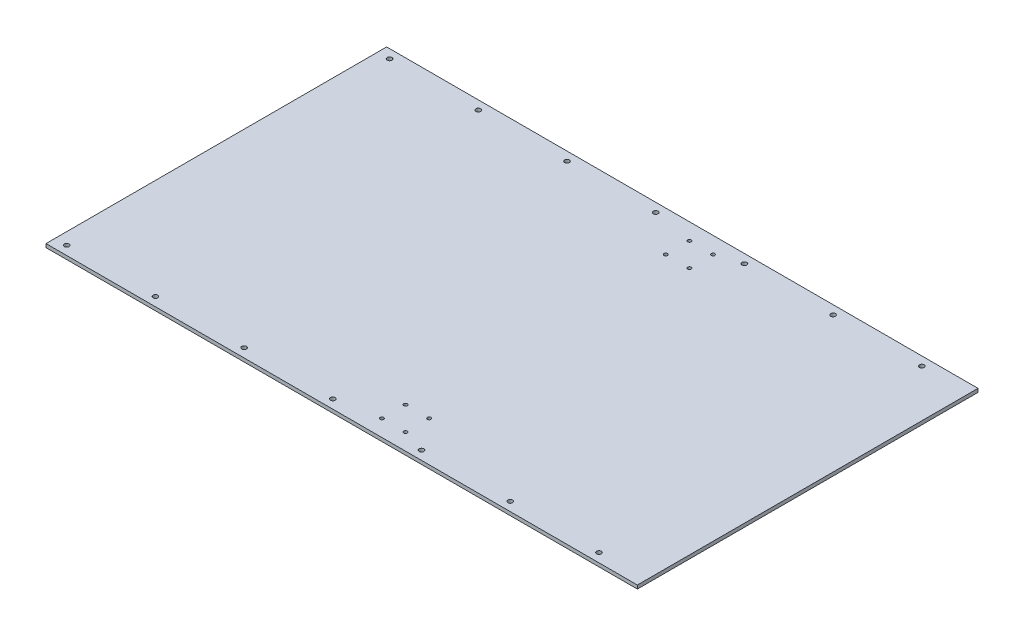
SolidWorks part; units mm, degrees
ref_plane "Front Plane" through (0, 0, 0) normal (0, 0, 1) x (1, 0, 0)
ref_plane "Top Plane" through (0, 0, 0) normal (0, 1, 0) x (1, 0, 0)
ref_plane "Right Plane" through (0, 0, 0) normal (1, 0, 0) x (0, 0, -1)
sketch "Sketch1" plane through (0, 0, 0) normal (0, 1, 0) x (1, 0, 0)
  line L1 (250, -144) -> (-250, -144)
  line L2 (250, -144) -> (250, 144)
  line L3 (250, 144) -> (-250, 144)
  line L4 (-250, -144) -> (-250, 144)
  line L5 (250, -144) -> (-250, 144) construction
  line L6 (250, 144) -> (-250, -144) construction
  point P0 (0, 0)
  dimension "D1" = 288
  dimension "D2" = 500
extrude "Boss-Extrude1" add sketch "Sketch1" along normal blind 3
sketch "Sketch2" plane through (0, 3, 0) normal (0, 1, 0) x (1, 0, 0)
  line L0 (250, 144) -> (-250, 144) construction
  line L1 (-250, 144) -> (-250, -144) construction
  line L2 (-1.65, 0) -> (1.65, 0) construction
  circle A0 centre (-240, 136.5) radius 2
  circle A1 centre (-165, 136.5) radius 2
  circle A2 centre (-90, 136.5) radius 2
  circle A3 centre (-15, 136.5) radius 2
  circle A4 centre (60, 136.5) radius 2
  circle A5 centre (135, 136.5) radius 2
  circle A6 centre (135, -136.5) radius 2
  circle A7 centre (60, -136.5) radius 2
  circle A8 centre (-15, -136.5) radius 2
  circle A9 centre (-90, -136.5) radius 2
  circle A10 centre (-165, -136.5) radius 2
  circle A11 centre (-240, -136.5) radius 2
  circle A12 centre (210, 136.5) radius 2
  circle A13 centre (210, -136.5) radius 2
  dimension "D1" = 7.5
  dimension "D2" = 10
  dimension "D4" = 75
  dimension "D5" = 75
  dimension "D3" = 6
extrude "Cut-Extrude1" cut sketch "Sketch2" against normal blind 10
sketch "Sketch3" plane through (0, 0, 0) normal (0, -1, 0) x (-1, 0, 0)
  circle A0 centre (-20, -110) radius 1.5
  circle A1 centre (-40, -110) radius 1.5
  circle A2 centre (-20, 110) radius 1.5
  circle A3 centre (-40, 110) radius 1.5
  circle A4 centre (-20, 130) radius 1.5
  circle A5 centre (-40, 130) radius 1.5
  circle A6 centre (-20, -130) radius 1.5
  circle A7 centre (-40, -130) radius 1.5
extrude "Cut-Extrude2" cut sketch "Sketch3" against normal blind 10
